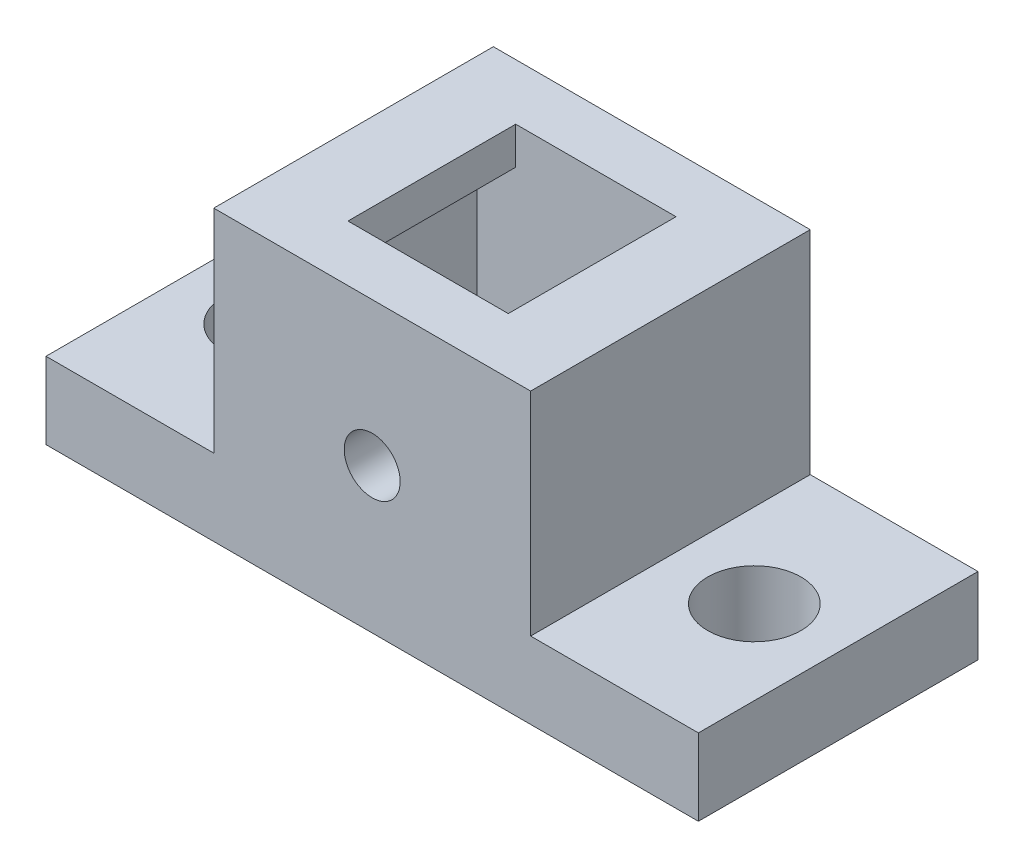
SolidWorks part; units mm, degrees
ref_plane "Front Plane" through (0, 0, 0) normal (0, 0, 1) x (1, 0, 0)
ref_plane "Top Plane" through (0, 0, 0) normal (0, 1, 0) x (1, 0, 0)
ref_plane "Right Plane" through (0, 0, 0) normal (1, 0, 0) x (0, 0, -1)
sketch "Sketch1" plane through (0, 0, 0) normal (0, 1, 0) x (1, 0, 0)
  line L1 (0, 0) -> (35, 0)
  line L2 (0, 0) -> (0, 15)
  line L3 (0, 15) -> (35, 15)
  line L4 (35, 0) -> (35, 15)
  dimension "D1" = 35
  dimension "D2" = 15
extrude "Boss-Extrude1" add sketch "Sketch1" along normal blind 23.49
sketch "Sketch2" plane through (0, 0, 0) normal (0, 0, 1) x (1, 0, 0)
  line L0 (26, 4.1073) -> (48.56, 4.1073)
  line L1 (-14.0053, 37.0075) -> (9, 37.0075)
  line L2 (-14.0053, 37.0075) -> (-14.0053, 4.1073)
  line L3 (-14.0053, 4.1073) -> (9, 4.1073)
  line L4 (48.56, 37.0075) -> (48.56, 4.1073)
  line L6 (9, 37.0075) -> (9, 4.1073)
  line L8 (26, 37.0075) -> (26, 4.1073)
  line L9 (26, 37.0075) -> (48.56, 37.0075)
  dimension "D1" = 9
  dimension "D2" = 9
extrude "Cut-Extrude1" cut sketch "Sketch2" against normal blind 23.49
sketch "Sketch3" plane through (0, 0, 0) normal (0, 0, 1) x (1, 0, 0)
  line L0 (9, 23.49) -> (26, 23.49) construction
  line L1 (9, 31.2216) -> (26, 31.2216)
  line L2 (9, 31.2216) -> (9, 15.49)
  line L3 (9, 15.49) -> (26, 15.49)
  line L4 (26, 31.2216) -> (26, 15.49)
  dimension "D1" = 0
  dimension "D2" = 0
  dimension "D3" = 8
extrude "Cut-Extrude2" cut sketch "Sketch3" against normal blind 23.49
sketch "Sketch4" plane through (0, 4.1073, 0) normal (0, 1, 0) x (1, 0, 0)
  line L4 (35, 7.5) -> (0, 7.5) construction
  line L5 (35, 15) -> (35, 0) construction
  line L6 (0, 0) -> (0, 15) construction
  circle A1 centre (4.5, 7.5) radius 2.5
  circle A3 centre (30.5, 7.5) radius 2.5
  point P8 (30.5, 7.5)
  point P11 (4.8241, 3.5)
  point P12 (-6.6977, 3.5)
  point P13 (5.1842, 3.5)
  point P14 (0, 0)
  point P15 (4.7727, 7.5)
  point P16 (4.5, 7.5)
  dimension "D2" = 5
  dimension "D4" = 5
sketch "Sketch5" plane through (0, 15.49, 0) normal (0, 1, 0) x (1, 0, 0)
  line L0 (26, 15) -> (26, 0) construction
  line L1 (13.2, 12) -> (21.8, 12)
  line L2 (13.2, 12) -> (13.2, 3)
  line L3 (13.2, 3) -> (21.8, 3)
  line L4 (21.8, 12) -> (21.8, 3)
  line L5 (9, 15) -> (26, 15) construction
  point P4 (17.5, 12)
  point P7 (13.2, 7.5)
  dimension "D1" = 8.6
  dimension "D2" = 8.5
  dimension "D3" = 9
  dimension "D4" = 7.5
extrude "Cut-Extrude4" cut sketch "Sketch5" against normal blind 12.5
sketch "Sketch8" plane through (0, 2.99, 0) normal (0, 1, 0) x (1, 0, 0)
  line L0 (11.1141, 3) -> (11.1141, 12)
  line L5 (11.1141, 3) -> (23.9569, 3)
  line L6 (23.9569, 3) -> (23.9569, 12)
  line L7 (11.1141, 12) -> (23.9569, 12)
  line L8 (13.2, 3) -> (21.8, 3) construction
  line L9 (21.8, 12) -> (13.2, 12) construction
  point P0 (17.5355, 12)
  point P1 (11.1141, 7.5)
  point P2 (17.5, 7.5)
extrude "Cut-Extrude5" cut sketch "Sketch8" along normal blind 10.5
extrude "Cut-Extrude6" cut sketch "Sketch4" against normal through all
sketch "Sketch9" plane through (0, 0, 0) normal (0, 0, 1) x (1, 0, 0)
  circle A0 centre (17.5, 7.7805) radius 1.5
  point P2 (17.1633, 8.5012)
  point P3 (17.5, 7.7805)
  dimension "D1" = 3
extrude "Cut-Extrude7" cut sketch "Sketch9" against normal through all
